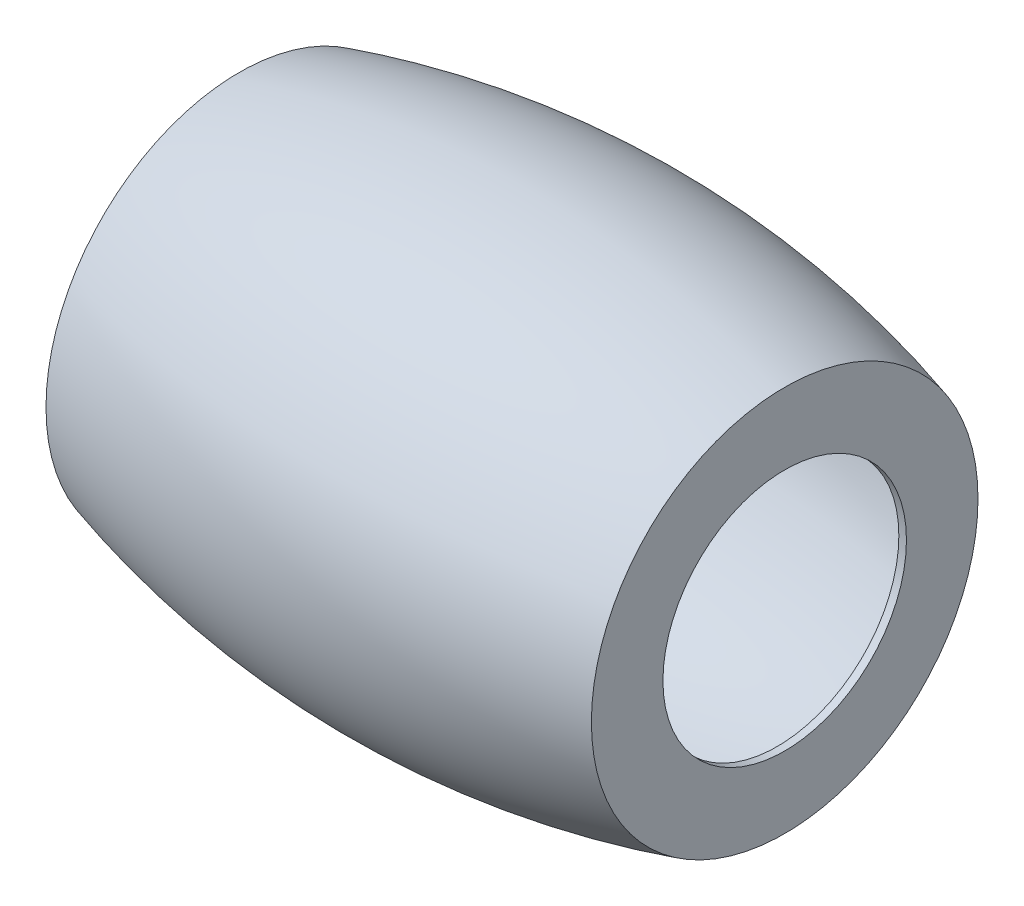
SolidWorks part; units mm, degrees
material "POLYURETHANE (11671)"
ref_plane "Front Plane" through (0, 0, 0) normal (0, 0, 1) x (1, 0, 0)
ref_plane "Top Plane" through (0, 0, 0) normal (0, 1, 0) x (1, 0, 0)
ref_plane "Right Plane" through (0, 0, 0) normal (1, 0, 0) x (0, 0, -1)
sketch "Sketch2" plane through (0, 0, 0) normal (0, 0, 1) x (1, 0, 0)
  line L0 (-17.9164, 0) -> (-17.9164, 12.7) construction
  line L1 (-17.9164, 8) -> (-17.9164, 12.7)
  line L2 (17.9164, 0) -> (17.9164, 12.7) construction
  line L3 (17.9164, 8) -> (17.9164, 12.7)
  line L4 (28.7417, 0) -> (-28.7417, 0) construction
  line L5 (17.9164, 0) -> (-17.9164, 0) construction
  line L6 (-17.4164, 0) -> (-17.4164, 12.3221) construction
  line L7 (-17.4164, 8) -> (-17.4164, 12.3221)
  line L8 (17.4164, 0) -> (17.4164, 12.3221) construction
  line L9 (17.4164, 8) -> (17.4164, 12.3221)
  line L10 (-17.4164, 8) -> (17.4164, 8) construction
  line L11 (-17.4164, 8) -> (-17.9164, 8)
  line L12 (17.4164, 8) -> (17.9164, 8)
  circle A0 centre (0, -49.782) radius 65 construction
  arc A1 (17.9164, 12.7) -> (-17.9164, 12.7) centre (0, -49.782) ccw
  circle A2 centre (0, -49.782) radius 64.5 construction
  arc A3 (17.4164, 12.3221) -> (-17.4164, 12.3221) centre (0, -49.782) ccw
  dimension "D1" = 8
revolve "Revolve1" add sketch "Sketch2" angle 360 about L5
